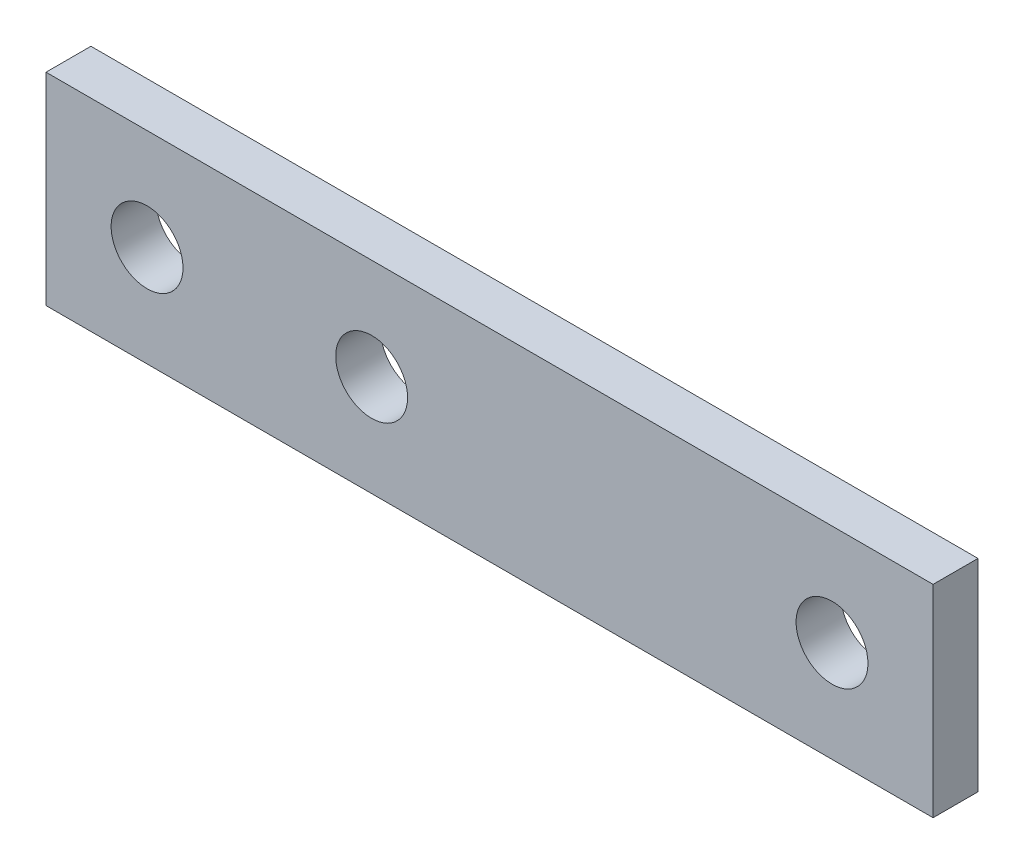
SolidWorks part; units mm, degrees
ref_plane "正面" through (0, 0, 0) normal (0, 0, 1) x (1, 0, 0)
ref_plane "平面" through (0, 0, 0) normal (0, 1, 0) x (1, 0, 0)
ref_plane "右側面" through (0, 0, 0) normal (1, 0, 0) x (0, 0, -1)
sketch "ｽｹｯﾁ1" plane through (0, 0, 0) normal (0, 0, 1) x (1, 0, 0)
  line L1 (-19.75, 4.5) -> (19.75, 4.5)
  line L2 (-19.75, 4.5) -> (-19.75, -4.5)
  line L3 (-19.75, -4.5) -> (19.75, -4.5)
  line L4 (19.75, 4.5) -> (19.75, -4.5)
  line L5 (-19.75, 4.5) -> (19.75, -4.5) construction
  line L6 (-19.75, -4.5) -> (19.75, 4.5) construction
  point P0 (0, 0)
  dimension "D1" = 39.5
  dimension "D2" = 9
extrude "ﾎﾞｽ - 押し出し1" add sketch "ｽｹｯﾁ1" along normal blind 2
sketch "ｽｹｯﾁ2" plane through (0, 0, 2) normal (0, 0, 1) x (1, 0, 0)
  line L0 (-19.75, 0) -> (-15.25, 0)
  line L1 (-19.75, 4.5) -> (-19.75, -4.5) construction
  line L2 (-15.25, 0) -> (-5.25, 0)
  line L3 (-5.25, 0) -> (15.25, 0)
  circle A0 centre (-15.25, 0) radius 1.6
  circle A1 centre (-5.25, 0) radius 1.6
  circle A2 centre (15.25, 0) radius 1.6
  dimension "D4" = 3.2
  dimension "D5" = 3.2
  dimension "D6" = 3.2
  dimension "D1" = 4.5
  dimension "D2" = 10
  dimension "D3" = 20.5
extrude "ｶｯﾄ - 押し出し1" cut sketch "ｽｹｯﾁ2" against normal blind 2
